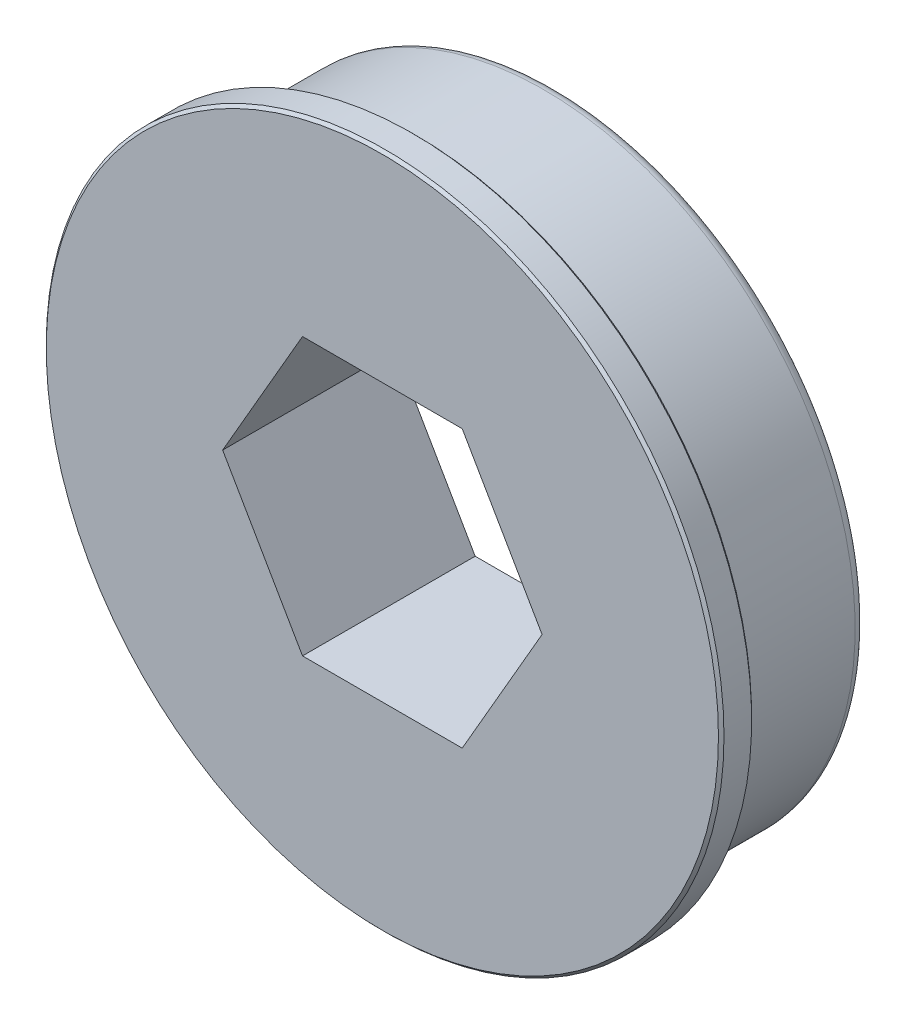
SolidWorks part; units mm, degrees
ref_plane "Front Plane" through (0, 0, 0) normal (0, 0, 1) x (1, 0, 0)
ref_plane "Top Plane" through (0, 0, 0) normal (0, 1, 0) x (1, 0, 0)
ref_plane "Right Plane" through (0, 0, 0) normal (1, 0, 0) x (0, 0, -1)
ref_plane "Plane1" through (0, 0, 0) normal (0, -1, 0) x (1, 0, 0)
sketch "Sketch1" plane through (0, 0, 0) normal (0, -1, 0) x (1, 0, 0)
  line L0 (15.5575, 7.9273) -> (0, 7.9273)
  line L1 (0, 7.9273) -> (0, 0)
  line L2 (0, 0) -> (14.2875, 0)
  line L3 (14.2875, 0) -> (14.2875, 5.8953)
  line L4 (14.2875, 5.8953) -> (13.97, 5.8953)
  line L5 (13.97, 5.8953) -> (13.97, 6.4033)
  line L6 (13.97, 6.4033) -> (15.5575, 6.4033)
  line L7 (15.5575, 6.4033) -> (15.5575, 7.9273)
  line L8 (0, 7.9273) -> (0, 0) construction
revolve "Revolve1" add sketch "Sketch1" angle 360 about L8
sketch "Sketch2" plane through (0, 0, 7.9273) normal (0, 0, 1) x (1, 0, 0)
  line L1 (7.3323, 0) -> (3.6662, 6.35)
  line L2 (3.6662, 6.35) -> (-3.6662, 6.35)
  line L3 (-3.6662, 6.35) -> (-7.3323, 0)
  line L4 (-7.3323, 0) -> (-3.6662, -6.35)
  line L5 (-3.6662, -6.35) -> (3.6662, -6.35)
  line L6 (3.6662, -6.35) -> (7.3323, 0)
  circle A0 centre (0, 0) radius 6.35 construction
  dimension "D1" = 12.7
extrude "Cut-Extrude1" cut sketch "Sketch2" against normal through all
chamfer "Chamfer1" distance 0.127 angle 45 2 edges at (-15.5575, 0, 6.4033) (-15.5575, 0, 7.9273)
fillet "Fillet1" radius 0.508 1 edges at (-14.2875, 0, 0)
